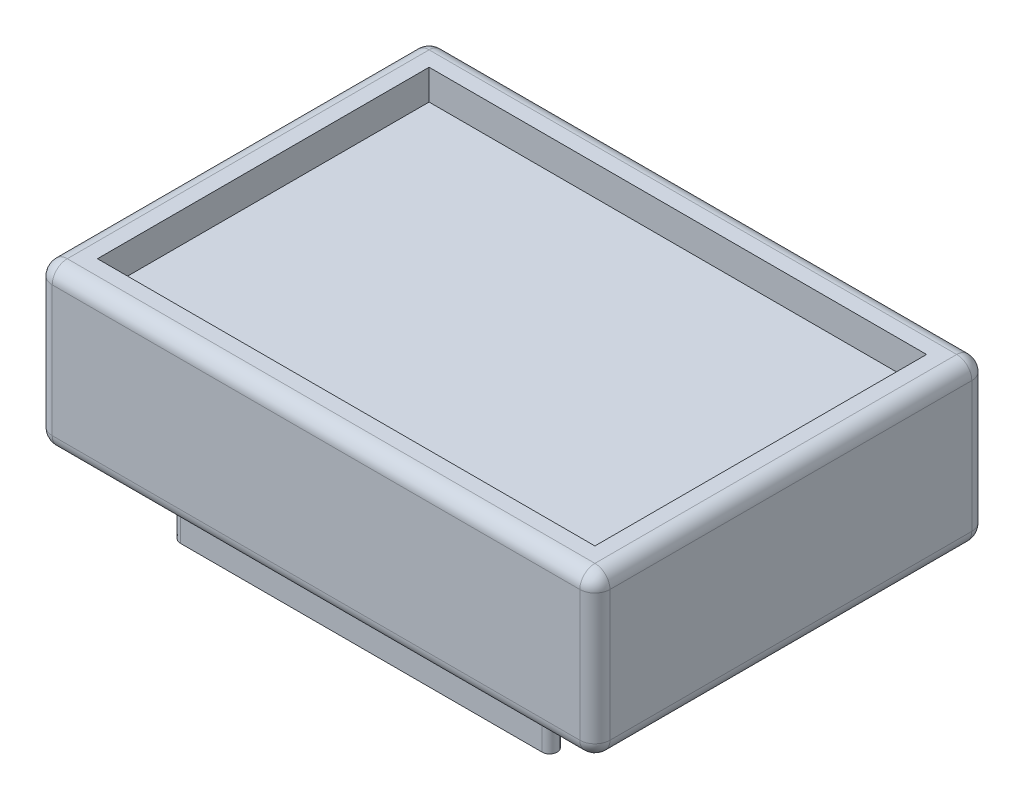
SolidWorks part; units mm, degrees
ref_plane "Front Plane" through (0, 0, 0) normal (0, 0, 1) x (1, 0, 0)
ref_plane "Top Plane" through (0, 0, 0) normal (0, 1, 0) x (1, 0, 0)
ref_plane "Right Plane" through (0, 0, 0) normal (1, 0, 0) x (0, 0, -1)
sketch "Sketch1" plane through (0, 0, 0) normal (0, 1, 0) x (1, 0, 0)
  line L0 (-46.99, 33.02) -> (46.99, 33.02)
  line L1 (-41.91, -27.94) -> (41.91, -27.94)
  line L2 (-41.91, -27.94) -> (-41.91, 27.94)
  line L3 (-41.91, 27.94) -> (41.91, 27.94)
  line L4 (41.91, -27.94) -> (41.91, 27.94)
  line L5 (0, 27.94) -> (0, -27.94) construction
  line L6 (-41.91, 0) -> (41.91, 0) construction
  line L7 (46.99, -33.02) -> (46.99, 33.02)
  line L8 (-46.99, -33.02) -> (46.99, -33.02)
  line L9 (-46.99, -33.02) -> (-46.99, 33.02)
  point P0 (0, 0)
  dimension "D1" = 83.82
  dimension "D2" = 55.88
  dimension "D3" = 5.08
extrude "Boss-Extrude1" add sketch "Sketch1" along normal blind 27.08 contours L2 L1 L4 L3 | L0 L7 L8 L9
sketch "Sketch3" plane through (0, 0, 0) normal (0, 1, 0) x (1, 0, 0)
  line L1 (-41.91, -27.94) -> (41.91, -27.94)
  line L2 (-41.91, -27.94) -> (-41.91, 27.94)
  line L3 (-41.91, 27.94) -> (41.91, 27.94)
  line L4 (41.91, -27.94) -> (41.91, 27.94)
  line L5 (0, 27.94) -> (0, -27.94) construction
  line L6 (-41.91, 0) -> (41.91, 0) construction
  point P0 (0, 0)
extrude "Boss-Extrude2" add sketch "Sketch3" along normal blind 22
sketch "Sketch4" plane through (0, 0, 0) normal (0, -1, 0) x (1, 0, 0)
  line L0 (-30.48, 24.13) -> (30.48, 24.13) construction
  line L1 (-30.48, 25.4) -> (30.48, 25.4)
  line L2 (-30.48, 22.86) -> (30.48, 22.86)
  line L3 (-46.99, 33.02) -> (46.99, 33.02) construction
  line L4 (-46.99, -33.02) -> (-46.99, 33.02) construction
  arc A0 (-30.48, 25.4) -> (-30.48, 22.86) centre (-30.48, 24.13) ccw
  arc A1 (30.48, 22.86) -> (30.48, 25.4) centre (30.48, 24.13) ccw
  point P2 (0, 24.13)
  point P9 (-31.75, 24.13)
  point P10 (31.75, 24.13)
  dimension "D4" = 1.27
  dimension "D1" = 7.62
  dimension "D2" = 63.5
  dimension "D3" = 46.99
extrude "Boss-Extrude3" add sketch "Sketch4" along normal blind 10
fillet "Fillet1" radius 2.54 12 edges at (-46.99, 27.08, 0) (-46.99, 0, 0) (0, 27.08, -33.02) (-46.99, 13.54, -33.02) (0, 0, -33.02) (46.99, 27.08, 0) (46.99, 13.54, -33.02) (46.99, 0, 0) (-46.99, 13.54, 33.02) (0, 27.08, 33.02) (46.99, 13.54, 33.02) (0, 0, 33.02)
